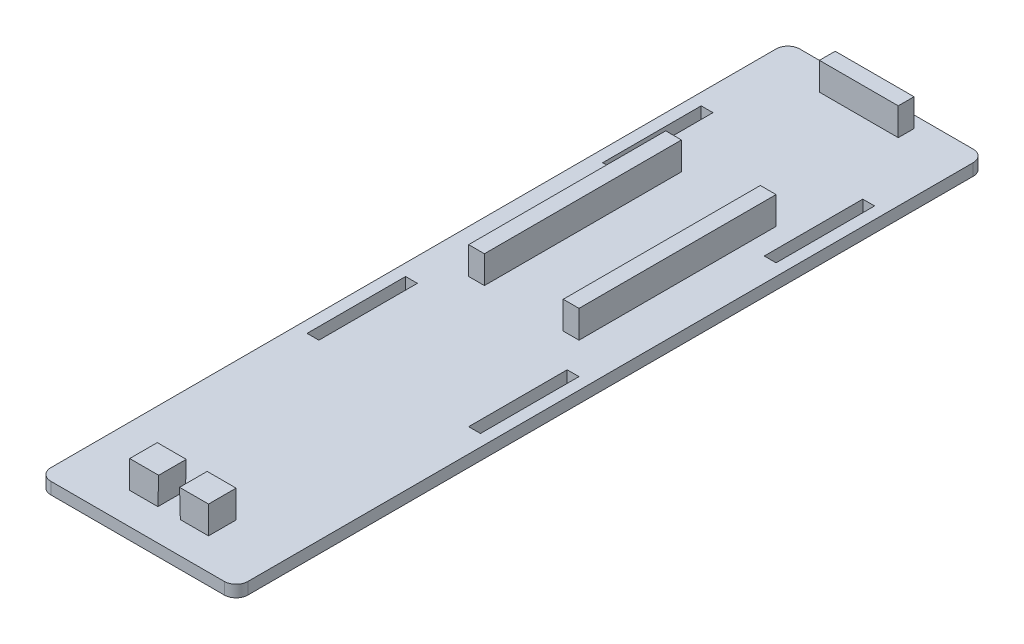
SolidWorks part; units mm, degrees
ref_plane "Front Plane" through (0, 0, 0) normal (0, 0, 1) x (1, 0, 0)
ref_plane "Top Plane" through (0, 0, 0) normal (0, 1, 0) x (1, 0, 0)
ref_plane "Right Plane" through (0, 0, 0) normal (1, 0, 0) x (0, 0, -1)
sketch "Sketch1" plane through (0, 0, 0) normal (0, 1, 0) x (1, 0, 0)
  line L1 (0, 0) -> (50, 0)
  line L2 (0, 0) -> (0, 190)
  line L3 (0, 190) -> (50, 190)
  line L4 (50, 0) -> (50, 190)
  dimension "D1" = 190
  dimension "D2" = 50
extrude "Boss-Extrude1" add sketch "Sketch1" along normal blind 3
fillet "Fillet1" radius 3 4 edges at (0, 1.5, -190) (50, 1.5, -190) (50, 1.5, 0) (0, 1.5, 0)
sketch "Sketch2" plane through (0, 3, 0) normal (0, 1, 0) x (1, 0, 0)
  line L0 (47, 190) -> (3, 190) construction
  line L1 (15, 187) -> (35, 187)
  line L2 (15, 187) -> (15, 183)
  line L3 (15, 183) -> (35, 183)
  line L4 (35, 187) -> (35, 183)
  line L5 (0, 187) -> (0, 3) construction
  line L8 (15, 148) -> (11, 148)
  line L9 (15, 148) -> (15, 98)
  line L10 (15, 98) -> (11, 98)
  line L11 (11, 148) -> (11, 98)
  line L12 (35, 148) -> (39, 148)
  line L13 (35, 148) -> (35, 98)
  line L14 (35, 98) -> (39, 98)
  line L15 (39, 148) -> (39, 98)
  dimension "D1" = 20
  dimension "D2" = 4
  dimension "D3" = 3
  dimension "D4" = 15
  dimension "D5" = 4
  dimension "D6" = 0
  dimension "D7" = 50
  dimension "D8" = 35
  dimension "D9" = 4
  dimension "D10" = 20
  dimension "D11" = 50
  dimension "D12" = 35
extrude "Boss-Extrude2" add sketch "Sketch2" along normal blind 7
sketch "Sketch3" plane through (0, 3, 0) normal (0, 1, 0) x (1, 0, 0)
  line L0 (50, 3) -> (50, 187) construction
  line L1 (15, 15) -> (35, 15)
  line L2 (15, 15) -> (15, 8)
  line L3 (15, 8) -> (35, 8)
  line L4 (35, 15) -> (35, 8)
  line L5 (3, 0) -> (47, 0) construction
  dimension "D1" = 20
  dimension "D2" = 15
  dimension "D3" = 7
  dimension "D4" = 8
extrude "Boss-Extrude3" add sketch "Sketch3" along normal blind 7
sketch "Sketch5" plane through (0, 0, -15) normal (0, 0, -1) x (-1, 0, 0)
  line L0 (-22.15, 3) -> (-22.35, 10)
  line L1 (-35, 3) -> (-15, 3) construction
  line L2 (-35, 10) -> (-15, 10) construction
  line L3 (-22.35, 10) -> (-27.65, 10)
  line L4 (-27.65, 10) -> (-27.85, 3)
  line L5 (-27.85, 3) -> (-22.15, 3)
  line L6 (-15, 10) -> (-15, 3) construction
  dimension "D1" = 5.7
  dimension "D2" = 5.3
  dimension "D3" = 7.15
  dimension "D4" = 7.35
extrude "Cut-Extrude1" cut sketch "Sketch5" against normal blind 7
sketch "Sketch6" plane through (0, 3, 0) normal (0, 1, 0) x (1, 0, 0)
  line L0 (47, 190) -> (3, 190) construction
  line L1 (3, 165) -> (6, 165)
  line L2 (3, 165) -> (3, 140)
  line L3 (3, 140) -> (6, 140)
  line L4 (6, 165) -> (6, 140)
  line L5 (0, 187) -> (0, 3) construction
  line L6 (50, 3) -> (50, 187) construction
  line L7 (44, 165) -> (47, 165)
  line L8 (44, 165) -> (44, 140)
  line L9 (44, 140) -> (47, 140)
  line L10 (47, 165) -> (47, 140)
  line L12 (3, 90) -> (6, 90)
  line L13 (3, 90) -> (3, 65)
  line L14 (3, 65) -> (6, 65)
  line L15 (6, 90) -> (6, 65)
  line L16 (44, 90) -> (47, 90)
  line L17 (44, 90) -> (44, 65)
  line L18 (44, 65) -> (47, 65)
  line L19 (47, 90) -> (47, 65)
  dimension "D1" = 3
  dimension "D2" = 25
  dimension "D3" = 25
  dimension "D4" = 3
  dimension "D5" = 3
  dimension "D6" = 3
  dimension "D7" = 25
  dimension "D8" = 25
  dimension "D9" = 25
  dimension "D10" = 50
  dimension "D11" = 3
  dimension "D12" = 3
  dimension "D13" = 3
  dimension "D14" = 3
  dimension "D15" = 25
  dimension "D16" = 50
extrude "Cut-Extrude2" cut sketch "Sketch6" against normal blind 7
